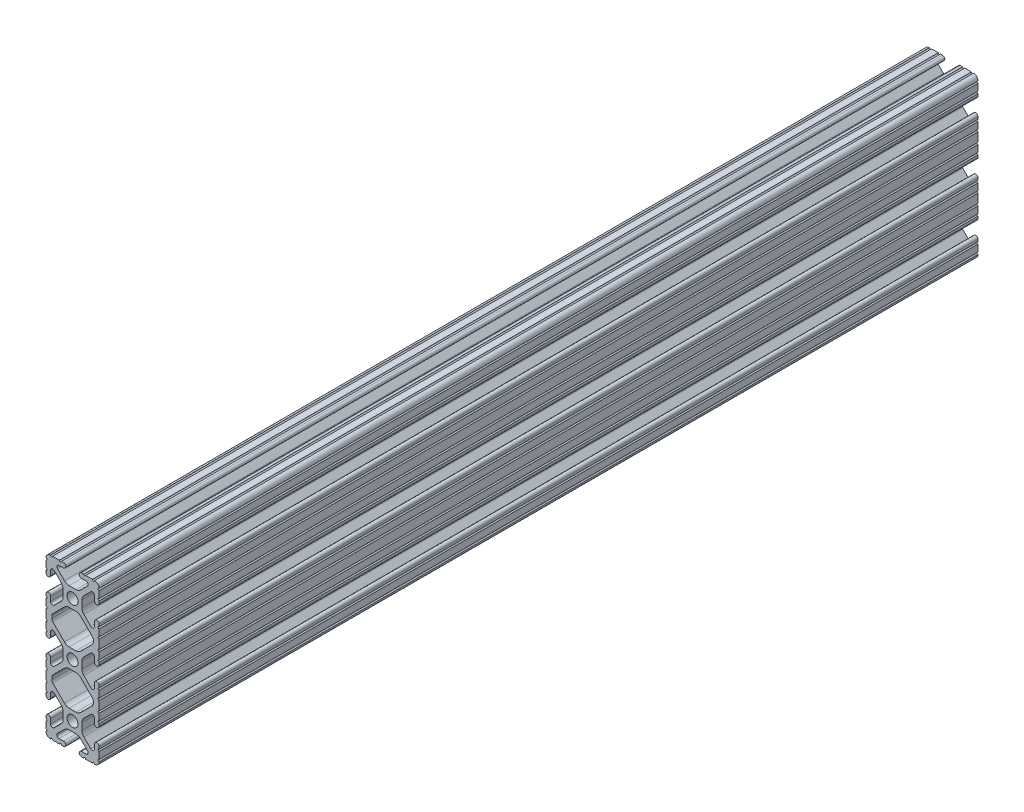
SolidWorks part; units mm, degrees
ref_plane "Front Plane" through (0, 0, 0) normal (0, 0, 1) x (1, 0, 0)
ref_plane "Top Plane" through (0, 0, 0) normal (0, 1, 0) x (1, 0, 0)
ref_plane "Right Plane" through (0, 0, 0) normal (1, 0, 0) x (0, 0, -1)
sketch "Sketch1" plane through (0, 0, 0) normal (0, 0, 1) x (1, 0, 0)
  line L0 (-9.9314, 12.1463) -> (-9.9314, 13.2537)
  line L1 (-9.4702, 14.3673) -> (-3.8759, 19.9616)
  line L2 (-1.6308, 20.8915) -> (1.6308, 20.8915)
  line L3 (3.8759, 19.9616) -> (9.4702, 14.3673)
  line L4 (9.9314, 13.2537) -> (9.9314, 12.1463)
  line L5 (9.4702, 11.0327) -> (3.8759, 5.4384)
  line L6 (1.6308, 4.5085) -> (-1.6308, 4.5085)
  line L7 (-3.8759, 5.4384) -> (-9.4702, 11.0327)
  line L8 (-9.9314, -13.2537) -> (-9.9314, -12.1463)
  line L9 (-9.4702, -11.0327) -> (-3.8759, -5.4384)
  line L10 (-1.6308, -4.5085) -> (1.6308, -4.5085)
  line L11 (3.8759, -5.4384) -> (9.4702, -11.0327)
  line L12 (9.9314, -12.1463) -> (9.9314, -13.2537)
  line L13 (9.4702, -14.3673) -> (3.8759, -19.9616)
  line L14 (1.6308, -20.8915) -> (-1.6308, -20.8915)
  line L15 (-3.8759, -19.9616) -> (-9.4702, -14.3673)
  line L16 (-6.3246, 38.1) -> (-9.5504, 38.1)
  line L17 (-12.7, 34.9504) -> (-12.7, 31.7246)
  line L18 (-12.7, 30.7086) -> (-12.7, 29.7023)
  line L19 (-10.4902, 29.7023) -> (-10.4902, 31.8748)
  line L20 (-8.7558, 32.5932) -> (-5.4384, 29.2759)
  line L21 (-4.5085, 27.0308) -> (-4.5085, 23.7692)
  line L22 (-5.4384, 21.5241) -> (-8.7558, 18.2068)
  line L23 (-10.4902, 18.9252) -> (-10.4902, 21.0977)
  line L24 (-12.7, 21.0977) -> (-12.7, 20.0914)
  line L25 (-12.7, 19.0754) -> (-12.7, 15.8496)
  line L26 (-12.7, 14.8336) -> (-12.7, 10.5664)
  line L27 (-12.7, 9.5504) -> (-12.7, 6.3246)
  line L28 (-12.7, 5.3086) -> (-12.7, 4.3023)
  line L29 (-10.4902, 4.3023) -> (-10.4902, 6.4748)
  line L30 (-8.7558, 7.1932) -> (-5.4384, 3.8759)
  line L31 (-4.5085, 1.6308) -> (-4.5085, -1.6308)
  line L32 (-5.4384, -3.8759) -> (-8.7558, -7.1932)
  line L33 (-10.4902, -6.4748) -> (-10.4902, -4.3023)
  line L34 (-12.7, -4.3023) -> (-12.7, -5.3086)
  line L35 (-12.7, -6.3246) -> (-12.7, -9.5504)
  line L36 (-12.7, -10.5664) -> (-12.7, -14.8336)
  line L37 (-12.7, -15.8496) -> (-12.7, -19.0754)
  line L38 (-12.7, -20.0914) -> (-12.7, -21.0977)
  line L39 (-10.4902, -21.0977) -> (-10.4902, -18.9252)
  line L40 (-8.7558, -18.2068) -> (-5.4384, -21.5241)
  line L41 (-4.5085, -23.7692) -> (-4.5085, -27.0308)
  line L42 (-5.4384, -29.2759) -> (-8.7558, -32.5932)
  line L43 (-10.4902, -31.8748) -> (-10.4902, -29.7023)
  line L44 (-12.7, -29.7023) -> (-12.7, -30.7086)
  line L45 (-12.7, -31.7246) -> (-12.7, -34.9504)
  line L46 (-9.5504, -38.1) -> (-6.3246, -38.1)
  line L47 (-5.3086, -38.1) -> (-4.3023, -38.1)
  line L48 (-4.3023, -35.8902) -> (-6.4748, -35.8902)
  line L49 (-7.1932, -34.1558) -> (-3.8759, -30.8384)
  line L50 (-1.6308, -29.9085) -> (1.6308, -29.9085)
  line L51 (3.8759, -30.8384) -> (7.1932, -34.1558)
  line L52 (6.4748, -35.8902) -> (4.3023, -35.8902)
  line L53 (4.3023, -38.1) -> (5.3086, -38.1)
  line L54 (6.3246, -38.1) -> (9.5504, -38.1)
  line L55 (12.7, -34.9504) -> (12.7, -31.7246)
  line L56 (12.7, -30.7086) -> (12.7, -29.7023)
  line L57 (10.4902, -29.7023) -> (10.4902, -31.8748)
  line L58 (8.7558, -32.5932) -> (5.4384, -29.2759)
  line L59 (4.5085, -27.0308) -> (4.5085, -23.7692)
  line L60 (5.4384, -21.5241) -> (8.7558, -18.2068)
  line L61 (10.4902, -18.9252) -> (10.4902, -21.0977)
  line L62 (12.7, -21.0977) -> (12.7, -20.0914)
  line L63 (12.7, -19.0754) -> (12.7, -15.8496)
  line L64 (12.7, -14.8336) -> (12.7, -10.5664)
  line L65 (12.7, -9.5504) -> (12.7, -6.3246)
  line L66 (12.7, -5.3086) -> (12.7, -4.3023)
  line L67 (10.4902, -4.3023) -> (10.4902, -6.4748)
  line L68 (8.7558, -7.1932) -> (5.4384, -3.8759)
  line L69 (4.5085, -1.6308) -> (4.5085, 1.6308)
  line L70 (5.4384, 3.8759) -> (8.7558, 7.1932)
  line L71 (10.4902, 6.4748) -> (10.4902, 4.3023)
  line L72 (12.7, 4.3023) -> (12.7, 5.3086)
  line L73 (12.7, 6.3246) -> (12.7, 9.5504)
  line L74 (12.7, 10.5664) -> (12.7, 14.8336)
  line L75 (12.7, 15.8496) -> (12.7, 19.0754)
  line L76 (12.7, 20.0914) -> (12.7, 21.0977)
  line L77 (10.4902, 21.0977) -> (10.4902, 18.9252)
  line L78 (8.7558, 18.2068) -> (5.4384, 21.5241)
  line L79 (4.5085, 23.7692) -> (4.5085, 27.0308)
  line L80 (5.4384, 29.2759) -> (8.7558, 32.5932)
  line L81 (10.4902, 31.8748) -> (10.4902, 29.7023)
  line L82 (12.7, 29.7023) -> (12.7, 30.7086)
  line L83 (12.7, 31.7246) -> (12.7, 34.9504)
  line L84 (9.5504, 38.1) -> (6.3246, 38.1)
  line L85 (5.3086, 38.1) -> (4.3023, 38.1)
  line L86 (4.3023, 35.8902) -> (6.4748, 35.8902)
  line L87 (7.1932, 34.1558) -> (3.8759, 30.8384)
  line L88 (1.6308, 29.9085) -> (-1.6308, 29.9085)
  line L89 (-3.8759, 30.8384) -> (-7.1932, 34.1558)
  line L90 (-6.4748, 35.8902) -> (-4.3023, 35.8902)
  line L91 (-4.3023, 38.1) -> (-5.3086, 38.1)
  circle A0 centre (0, 25.4) radius 2.6035
  arc A1 (-9.9314, 13.2537) -> (-9.4702, 14.3673) centre (-8.3566, 13.2537) cw
  arc A2 (-3.8759, 19.9616) -> (-1.6308, 20.8915) centre (-1.6308, 17.7165) cw
  arc A3 (1.6308, 20.8915) -> (3.8759, 19.9616) centre (1.6308, 17.7165) cw
  arc A4 (9.4702, 14.3673) -> (9.9314, 13.2537) centre (8.3566, 13.2537) cw
  arc A5 (9.9314, 12.1463) -> (9.4702, 11.0327) centre (8.3566, 12.1463) cw
  arc A6 (3.8759, 5.4384) -> (1.6308, 4.5085) centre (1.6308, 7.6835) cw
  arc A7 (-1.6308, 4.5085) -> (-3.8759, 5.4384) centre (-1.6308, 7.6835) cw
  arc A8 (-9.4702, 11.0327) -> (-9.9314, 12.1463) centre (-8.3566, 12.1463) cw
  arc A9 (-9.9314, -12.1463) -> (-9.4702, -11.0327) centre (-8.3566, -12.1463) cw
  arc A10 (-3.8759, -5.4384) -> (-1.6308, -4.5085) centre (-1.6308, -7.6835) cw
  arc A11 (1.6308, -4.5085) -> (3.8759, -5.4384) centre (1.6308, -7.6835) cw
  arc A12 (9.4702, -11.0327) -> (9.9314, -12.1463) centre (8.3566, -12.1463) cw
  arc A13 (9.9314, -13.2537) -> (9.4702, -14.3673) centre (8.3566, -13.2537) cw
  arc A14 (3.8759, -19.9616) -> (1.6308, -20.8915) centre (1.6308, -17.7165) cw
  arc A15 (-1.6308, -20.8915) -> (-3.8759, -19.9616) centre (-1.6308, -17.7165) cw
  arc A16 (-9.4702, -14.3673) -> (-9.9314, -13.2537) centre (-8.3566, -13.2537) cw
  circle A17 centre (0, -25.4) radius 2.6035
  circle A18 centre (0, 0) radius 2.6035
  arc A19 (-5.3086, 38.1) -> (-6.3246, 38.1) centre (-5.8166, 38.1) cw
  arc A20 (-9.5504, 38.1) -> (-10.5664, 38.1) centre (-10.0584, 38.1) cw
  arc A21 (-10.5664, 38.1) -> (-12.7, 35.9664) centre (-10.592, 35.992) ccw
  arc A22 (-12.7, 35.9664) -> (-12.7, 34.9504) centre (-12.7, 35.4584) cw
  arc A23 (-12.7, 31.7246) -> (-12.7, 30.7086) centre (-12.7, 31.2166) cw
  arc A24 (-12.7, 29.7023) -> (-10.4902, 29.7023) centre (-11.5951, 29.7023) ccw
  arc A25 (-10.4902, 31.8748) -> (-8.7558, 32.5932) centre (-9.4742, 31.8748) cw
  arc A26 (-5.4384, 29.2759) -> (-4.5085, 27.0308) centre (-7.6835, 27.0308) cw
  arc A27 (-4.5085, 23.7692) -> (-5.4384, 21.5241) centre (-7.6835, 23.7692) cw
  arc A28 (-8.7558, 18.2068) -> (-10.4902, 18.9252) centre (-9.4742, 18.9252) cw
  arc A29 (-10.4902, 21.0977) -> (-12.7, 21.0977) centre (-11.5951, 21.0977) ccw
  arc A30 (-12.7, 20.0914) -> (-12.7, 19.0754) centre (-12.7, 19.5834) cw
  arc A31 (-12.7, 15.8496) -> (-12.7, 14.8336) centre (-12.7, 15.3416) cw
  arc A32 (-12.7, 10.5664) -> (-12.7, 9.5504) centre (-12.7, 10.0584) cw
  arc A33 (-12.7, 6.3246) -> (-12.7, 5.3086) centre (-12.7, 5.8166) cw
  arc A34 (-12.7, 4.3023) -> (-10.4902, 4.3023) centre (-11.5951, 4.3023) ccw
  arc A35 (-10.4902, 6.4748) -> (-8.7558, 7.1932) centre (-9.4742, 6.4748) cw
  arc A36 (-5.4384, 3.8759) -> (-4.5085, 1.6308) centre (-7.6835, 1.6308) cw
  arc A37 (-4.5085, -1.6308) -> (-5.4384, -3.8759) centre (-7.6835, -1.6308) cw
  arc A38 (-8.7558, -7.1932) -> (-10.4902, -6.4748) centre (-9.4742, -6.4748) cw
  arc A39 (-10.4902, -4.3023) -> (-12.7, -4.3023) centre (-11.5951, -4.3023) ccw
  arc A40 (-12.7, -5.3086) -> (-12.7, -6.3246) centre (-12.7, -5.8166) cw
  arc A41 (-12.7, -9.5504) -> (-12.7, -10.5664) centre (-12.7, -10.0584) cw
  arc A42 (-12.7, -14.8336) -> (-12.7, -15.8496) centre (-12.7, -15.3416) cw
  arc A43 (-12.7, -19.0754) -> (-12.7, -20.0914) centre (-12.7, -19.5834) cw
  arc A44 (-12.7, -21.0977) -> (-10.4902, -21.0977) centre (-11.5951, -21.0977) ccw
  arc A45 (-10.4902, -18.9252) -> (-8.7558, -18.2068) centre (-9.4742, -18.9252) cw
  arc A46 (-5.4384, -21.5241) -> (-4.5085, -23.7692) centre (-7.6835, -23.7692) cw
  arc A47 (-4.5085, -27.0308) -> (-5.4384, -29.2759) centre (-7.6835, -27.0308) cw
  arc A48 (-8.7558, -32.5932) -> (-10.4902, -31.8748) centre (-9.4742, -31.8748) cw
  arc A49 (-10.4902, -29.7023) -> (-12.7, -29.7023) centre (-11.5951, -29.7023) ccw
  arc A50 (-12.7, -30.7086) -> (-12.7, -31.7246) centre (-12.7, -31.2166) cw
  arc A51 (-12.7, -34.9504) -> (-12.7, -35.9664) centre (-12.7, -35.4584) cw
  arc A52 (-12.7, -35.9664) -> (-10.5664, -38.1) centre (-10.592, -35.992) ccw
  arc A53 (-10.5664, -38.1) -> (-9.5504, -38.1) centre (-10.0584, -38.1) cw
  arc A54 (-6.3246, -38.1) -> (-5.3086, -38.1) centre (-5.8166, -38.1) cw
  arc A55 (-4.3023, -38.1) -> (-4.3023, -35.8902) centre (-4.3023, -36.9951) ccw
  arc A56 (-6.4748, -35.8902) -> (-7.1932, -34.1558) centre (-6.4748, -34.8742) cw
  arc A57 (-3.8759, -30.8384) -> (-1.6308, -29.9085) centre (-1.6308, -33.0835) cw
  arc A58 (1.6308, -29.9085) -> (3.8759, -30.8384) centre (1.6308, -33.0835) cw
  arc A59 (7.1932, -34.1558) -> (6.4748, -35.8902) centre (6.4748, -34.8742) cw
  arc A60 (4.3023, -35.8902) -> (4.3023, -38.1) centre (4.3023, -36.9951) ccw
  arc A61 (5.3086, -38.1) -> (6.3246, -38.1) centre (5.8166, -38.1) cw
  arc A62 (9.5504, -38.1) -> (10.5664, -38.1) centre (10.0584, -38.1) cw
  arc A63 (10.5664, -38.1) -> (12.7, -35.9664) centre (10.592, -35.992) ccw
  arc A64 (12.7, -35.9664) -> (12.7, -34.9504) centre (12.7, -35.4584) cw
  arc A65 (12.7, -31.7246) -> (12.7, -30.7086) centre (12.7, -31.2166) cw
  arc A66 (12.7, -29.7023) -> (10.4902, -29.7023) centre (11.5951, -29.7023) ccw
  arc A67 (10.4902, -31.8748) -> (8.7558, -32.5932) centre (9.4742, -31.8748) cw
  arc A68 (5.4384, -29.2759) -> (4.5085, -27.0308) centre (7.6835, -27.0308) cw
  arc A69 (4.5085, -23.7692) -> (5.4384, -21.5241) centre (7.6835, -23.7692) cw
  arc A70 (8.7558, -18.2068) -> (10.4902, -18.9252) centre (9.4742, -18.9252) cw
  arc A71 (10.4902, -21.0977) -> (12.7, -21.0977) centre (11.5951, -21.0977) ccw
  arc A72 (12.7, -20.0914) -> (12.7, -19.0754) centre (12.7, -19.5834) cw
  arc A73 (12.7, -15.8496) -> (12.7, -14.8336) centre (12.7, -15.3416) cw
  arc A74 (12.7, -10.5664) -> (12.7, -9.5504) centre (12.7, -10.0584) cw
  arc A75 (12.7, -6.3246) -> (12.7, -5.3086) centre (12.7, -5.8166) cw
  arc A76 (12.7, -4.3023) -> (10.4902, -4.3023) centre (11.5951, -4.3023) ccw
  arc A77 (10.4902, -6.4748) -> (8.7558, -7.1932) centre (9.4742, -6.4748) cw
  arc A78 (5.4384, -3.8759) -> (4.5085, -1.6308) centre (7.6835, -1.6308) cw
  arc A79 (4.5085, 1.6308) -> (5.4384, 3.8759) centre (7.6835, 1.6308) cw
  arc A80 (8.7558, 7.1932) -> (10.4902, 6.4748) centre (9.4742, 6.4748) cw
  arc A81 (10.4902, 4.3023) -> (12.7, 4.3023) centre (11.5951, 4.3023) ccw
  arc A82 (12.7, 5.3086) -> (12.7, 6.3246) centre (12.7, 5.8166) cw
  arc A83 (12.7, 9.5504) -> (12.7, 10.5664) centre (12.7, 10.0584) cw
  arc A84 (12.7, 14.8336) -> (12.7, 15.8496) centre (12.7, 15.3416) cw
  arc A85 (12.7, 19.0754) -> (12.7, 20.0914) centre (12.7, 19.5834) cw
  arc A86 (12.7, 21.0977) -> (10.4902, 21.0977) centre (11.5951, 21.0977) ccw
  arc A87 (10.4902, 18.9252) -> (8.7558, 18.2068) centre (9.4742, 18.9252) cw
  arc A88 (5.4384, 21.5241) -> (4.5085, 23.7692) centre (7.6835, 23.7692) cw
  arc A89 (4.5085, 27.0308) -> (5.4384, 29.2759) centre (7.6835, 27.0308) cw
  arc A90 (8.7558, 32.5932) -> (10.4902, 31.8748) centre (9.4742, 31.8748) cw
  arc A91 (10.4902, 29.7023) -> (12.7, 29.7023) centre (11.5951, 29.7023) ccw
  arc A92 (12.7, 30.7086) -> (12.7, 31.7246) centre (12.7, 31.2166) cw
  arc A93 (12.7, 34.9504) -> (12.7, 35.9664) centre (12.7, 35.4584) cw
  arc A94 (12.7, 35.9664) -> (10.5664, 38.1) centre (10.592, 35.992) ccw
  arc A95 (10.5664, 38.1) -> (9.5504, 38.1) centre (10.0584, 38.1) cw
  arc A96 (6.3246, 38.1) -> (5.3086, 38.1) centre (5.8166, 38.1) cw
  arc A97 (4.3023, 38.1) -> (4.3023, 35.8902) centre (4.3023, 36.9951) ccw
  arc A98 (6.4748, 35.8902) -> (7.1932, 34.1558) centre (6.4748, 34.8742) cw
  arc A99 (3.8759, 30.8384) -> (1.6308, 29.9085) centre (1.6308, 33.0835) cw
  arc A100 (-1.6308, 29.9085) -> (-3.8759, 30.8384) centre (-1.6308, 33.0835) cw
  arc A101 (-7.1932, 34.1558) -> (-6.4748, 35.8902) centre (-6.4748, 34.8742) cw
  arc A102 (-4.3023, 35.8902) -> (-4.3023, 38.1) centre (-4.3023, 36.9951) ccw
extrude "Boss-Extrude1" add sketch "Sketch1" against normal blind 420.6875
